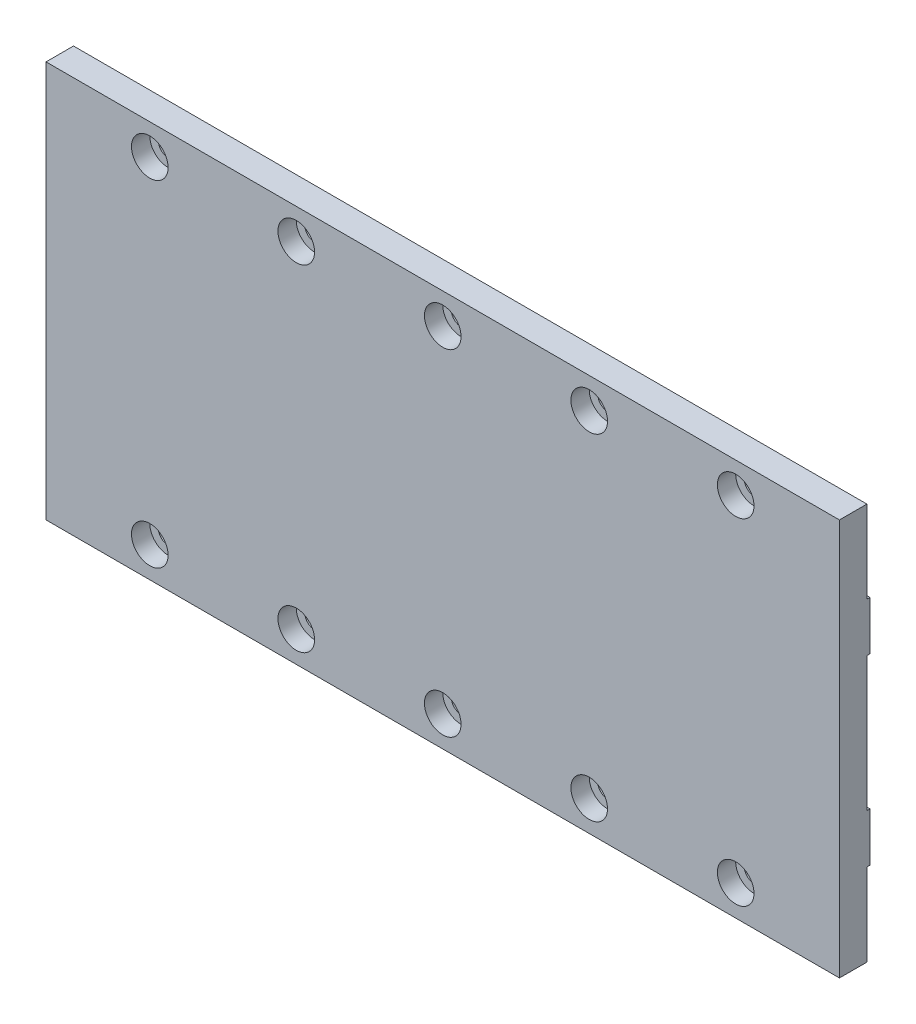
SolidWorks part; units mm, degrees
ref_plane "Plan de face" through (0, 0, 0) normal (0, 0, 1) x (1, 0, 0)
ref_plane "Plan de dessus" through (0, 0, 0) normal (0, 1, 0) x (1, 0, 0)
ref_plane "Plan de droite" through (0, 0, 0) normal (1, 0, 0) x (0, 0, -1)
sketch "Esquisse1" plane through (0, 0, 0) normal (0, 0, 1) x (1, 0, 0)
  line L1 (0, 0) -> (130, 0)
  line L2 (0, 0) -> (0, 65)
  line L3 (0, 65) -> (130, 65)
  line L4 (130, 0) -> (130, 65)
  circle A0 centre (113, 5) radius 1.6
  circle A1 centre (89, 5) radius 1.6
  circle A2 centre (65, 5) radius 1.6
  circle A3 centre (41, 5) radius 1.6
  circle A4 centre (17, 5) radius 1.6
  circle A5 centre (113, 60) radius 1.6
  circle A6 centre (89, 60) radius 1.6
  circle A7 centre (65, 60) radius 1.6
  circle A8 centre (41, 60) radius 1.6
  circle A9 centre (17, 60) radius 1.6
  point P27 (102.0384, 68.9636)
  point P28 (36.7354, 61.0422)
  dimension "D3" = 17
  dimension "D14" = 17
  dimension "D1" = 130
  dimension "D2" = 65
  dimension "D4" = 24
  dimension "D5" = 24
  dimension "D6" = 24
  dimension "D7" = 24
  dimension "D8" = 5
  dimension "D9" = 5
  dimension "D10" = 5
  dimension "D11" = 5
  dimension "D12" = 5
  dimension "D13" = 17
  dimension "D15" = 24
  dimension "D16" = 24
  dimension "D17" = 24
  dimension "D18" = 24
  dimension "D19" = 5
  dimension "D20" = 5
  dimension "D21" = 5
  dimension "D22" = 5
  dimension "D23" = 5
extrude "Boss.-Extru.1" add sketch "Esquisse1" along normal blind 5
sketch "Esquisse2" plane through (0, 0, 0) normal (0, 0, -1) x (-1, 0, 0)
  line L0 (0, 65) -> (0, 0) construction
  line L1 (-130, 65) -> (0, 65)
  line L2 (-130, 65) -> (-130, 51.5)
  line L3 (-130, 51.5) -> (0, 51.5)
  line L4 (0, 65) -> (0, 51.5)
  line L5 (-130, 0) -> (-130, 65) construction
  line L6 (0, 0) -> (-130, 0)
  line L7 (0, 0) -> (0, 13.5)
  line L8 (0, 13.5) -> (-130, 13.5)
  line L9 (-130, 0) -> (-130, 13.5)
  line L11 (-130, 43.5) -> (0, 43.5)
  line L12 (-130, 43.5) -> (-130, 21.5)
  line L13 (-130, 21.5) -> (0, 21.5)
  line L14 (0, 43.5) -> (0, 21.5)
  dimension "D1" = 13.5
  dimension "D2" = 8
  dimension "D3" = 8
  dimension "D4" = 13.5
extrude "Enlèv. mat.-Extru.1" cut sketch "Esquisse2" against normal blind 0.5
sketch "Esquisse3" plane through (0, 0, 5) normal (0, 0, 1) x (1, 0, 0)
  circle A0 centre (17, 60) radius 3
  circle A1 centre (41, 60) radius 3
  circle A2 centre (65, 60) radius 3
  circle A3 centre (89, 60) radius 3
  circle A4 centre (113, 60) radius 3
  circle A5 centre (113, 5) radius 3
  circle A6 centre (89, 5) radius 3
  circle A7 centre (65, 5) radius 3
  circle A8 centre (41, 5) radius 3
  circle A9 centre (17, 5) radius 3
extrude "Enlèv. mat.-Extru.2" cut sketch "Esquisse3" against normal blind 3
